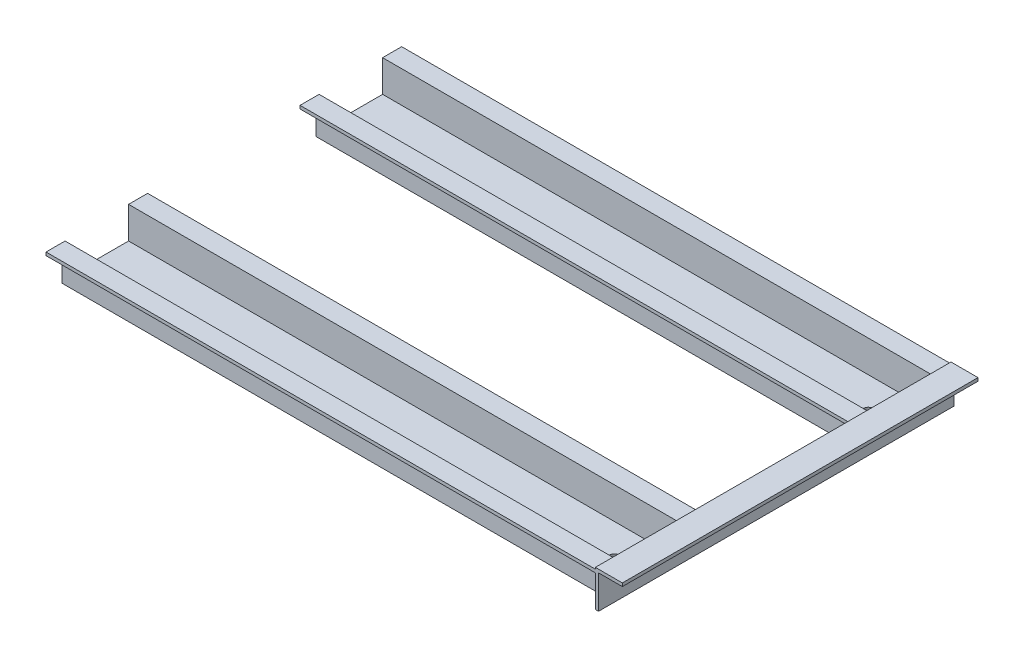
SolidWorks part; units mm, degrees
material "AISI 304"
ref_plane "Front Plane" through (0, 0, 0) normal (1, 0, 0) x (0, 1, 0)
ref_plane "Top Plane" through (0, 0, 0) normal (0, 0, 1) x (0, 1, 0)
ref_plane "Right Plane" through (0, 0, 0) normal (0, 1, 0) x (-1, 0, 0)
ref_plane "Plane1" through (-346, 0, 0) normal (-1, 0, 0) x (0, 1, 0)
sketch "Sketch2" plane through (0, 0, 0) normal (1, 0, 0) x (0, 1, 0)
  line L0 (20, 112) -> (20, 102)
  line L1 (20, 102) -> (0, 102)
  line L2 (0, 102) -> (0, 58)
  line L3 (-32.698, 80) -> (83.4362, 80) construction
  line L4 (20, 48) -> (20, 58)
  line L5 (20, 58) -> (0, 58)
  point P10 (0, 80)
  dimension "D1" = 112
  dimension "D2" = 80
  dimension "D3" = 10
  dimension "D4" = 20
extrude "Extrude-Thin1" add sketch "Sketch2" against normal up to surface (346 mm away) thin up to plane "Plane1" thin type one direction wall 2
sketch "Sketch5" plane through (0, 2, 0) normal (0, 1, 0) x (-1, 0, 0)
  line L0 (289.2666, 80) -> (331.9816, 80) construction
  line L1 (0, 60) -> (0, 100) construction
  line L2 (346, -12.65) -> (346, 12.65) construction
  circle A0 centre (326, 80) radius 3.3
  point P6 (0, 80)
  dimension "D1" = 6.6
  dimension "D2" = 20
extrude "Cut-Extrude1" cut sketch "Sketch5" against normal through all both and the other way through all contours A0
mirror "Mirror1" about plane through (0, 0, 0) normal (0, 0, 1) of bodies 103
sketch "Sketch6" plane through (-346, 0, 0) normal (-1, 0, 0) x (0, 1, 0)
  line L1 (23, 112) -> (0, 112)
  line L2 (23, 112) -> (23, -112)
  line L3 (23, -112) -> (0, -112)
  line L4 (0, 112) -> (0, -112)
  line L5 (0, -58) -> (0, -102) construction
  line L6 (20, -112) -> (22, -112) construction
  line L7 (20, 112) -> (22, 112) construction
  line L8 (22, -100) -> (22, -112) construction
  dimension "D1" = 1
extrude "Boss-Extrude2" add sketch "Sketch6" along normal blind 2
sketch "Sketch8" plane through (-348, 0, 0) normal (-1, 0, 0) x (0, -1, 0)
  line L0 (-23, 112) -> (-23, -112) construction
  line L1 (-23, 112) -> (-23, -112)
extrude "Extrude-Thin2" add sketch "Sketch8" along normal blind 15 thin thin type one direction reverse wall 2
mirror "Mirror2" about plane through (0, 0, 0) normal (1, 0, 0) of bodies 106
other "SurfaceCut1"
